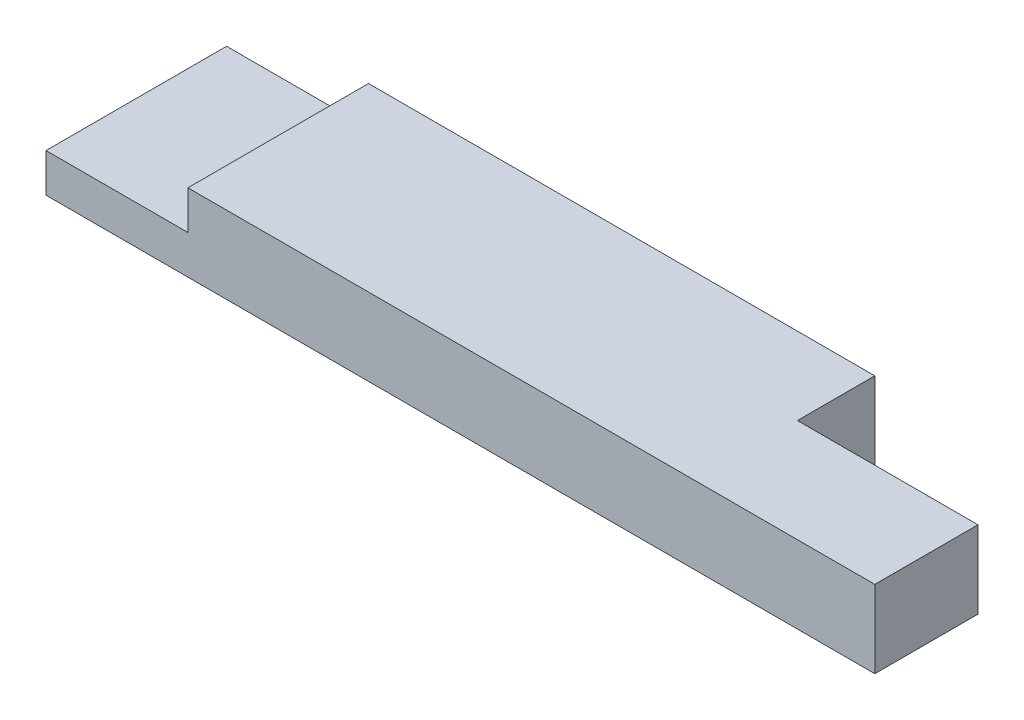
SolidWorks part; units mm, degrees
material "Pine"
ref_plane "Front Plane" through (0, 0, 0) normal (0, 0, 1) x (1, 0, 0)
ref_plane "Top Plane" through (0, 0, 0) normal (0, 1, 0) x (1, 0, 0)
ref_plane "Right Plane" through (0, 0, 0) normal (1, 0, 0) x (0, 0, -1)
sketch "Sketch1" plane through (0, 0, 0) normal (0, 1, 0) x (1, 0, 0)
  line L1 (0, 0) -> (407.9875, 0)
  line L2 (0, 0) -> (0, 88.9)
  line L3 (0, 88.9) -> (407.9875, 88.9)
  line L4 (407.9875, 0) -> (407.9875, 88.9)
  dimension "D1" = 88.9
  dimension "D2" = 407.9875
extrude "Boss-Extrude1" add sketch "Sketch1" along normal blind 38.1
sketch "Sketch3" plane through (0, 38.1, 0) normal (0, 1, 0) x (1, 0, 0)
  line L1 (407.9875, 88.9) -> (319.0875, 88.9)
  line L2 (407.9875, 88.9) -> (407.9875, 50.8)
  line L3 (407.9875, 50.8) -> (319.0875, 50.8)
  line L4 (319.0875, 88.9) -> (319.0875, 50.8)
  dimension "D1" = 88.9
  dimension "D2" = 38.1
extrude "Cut-Extrude2" cut sketch "Sketch3" against normal through all
sketch "Sketch4" plane through (0, 0, -88.9) normal (0, 0, -1) x (-1, 0, 0)
  line L0 (0, 38.1) -> (0, 0) construction
  line L1 (-69.85, 38.1) -> (0, 38.1)
  line L2 (-69.85, 38.1) -> (-69.85, 19.05)
  line L3 (-69.85, 19.05) -> (0, 19.05)
  line L4 (0, 38.1) -> (0, 19.05)
  dimension "D1" = 19.05
  dimension "D2" = 69.85
extrude "Cut-Extrude3" cut sketch "Sketch4" against normal through all
